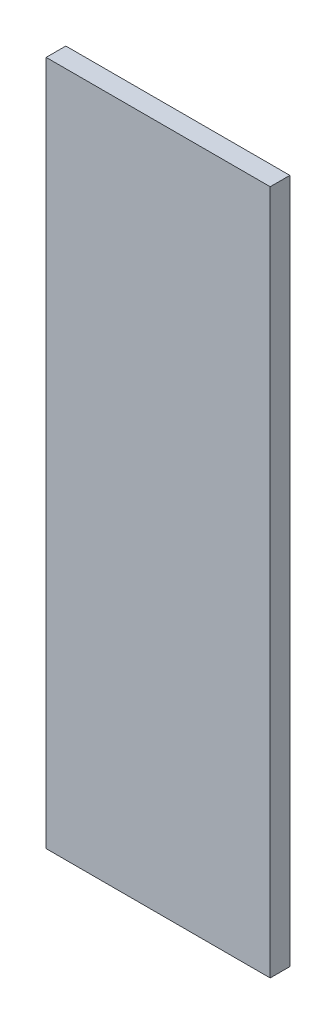
SolidWorks part; units mm, degrees
ref_plane "Front Plane" through (0, 0, 0) normal (0, 0, 1) x (1, 0, 0)
ref_plane "Top Plane" through (0, 0, 0) normal (0, 1, 0) x (1, 0, 0)
ref_plane "Right Plane" through (0, 0, 0) normal (1, 0, 0) x (0, 0, -1)
sketch "Sketch1" plane through (0, 0, 0) normal (0, 0, 1) x (1, 0, 0)
  line L1 (102.5, -313.5) -> (-102.5, -313.5)
  line L2 (102.5, -313.5) -> (102.5, 313.5)
  line L3 (102.5, 313.5) -> (-102.5, 313.5)
  line L4 (-102.5, -313.5) -> (-102.5, 313.5)
  line L5 (102.5, -313.5) -> (-102.5, 313.5) construction
  line L6 (102.5, 313.5) -> (-102.5, -313.5) construction
  point P0 (0, 0)
  dimension "D1" = 627
  dimension "D2" = 205
extrude "Boss-Extrude1" add sketch "Sketch1" along normal blind 18
equation "\"H_DSP\"=18"
equation "\"D1@Boss-Extrude1\"=\"H_DSP\""
